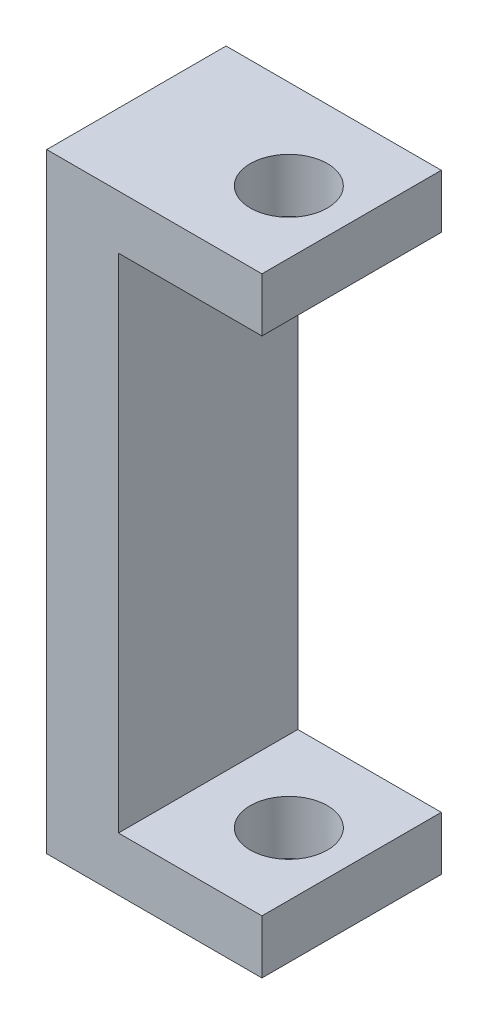
SolidWorks part; units mm, degrees
ref_plane "Front Plane" through (0, 0, 0) normal (0, 0, 1) x (1, 0, 0)
ref_plane "Top Plane" through (0, 0, 0) normal (0, 1, 0) x (1, 0, 0)
ref_plane "Right Plane" through (0, 0, 0) normal (1, 0, 0) x (0, 0, -1)
sketch "Sketch1" plane through (0, 0, 0) normal (0, 0, 1) x (1, 0, 0)
  line L1 (6, -17) -> (-6, -17)
  line L2 (6, -17) -> (6, 17)
  line L3 (6, 17) -> (-6, 17)
  line L4 (-6, -17) -> (-6, 17)
  line L5 (6, -17) -> (-6, 17) construction
  line L6 (6, 17) -> (-6, -17) construction
  point P0 (0, 0)
  dimension "D1" = 34
  dimension "D2" = 12
extrude "Boss-Extrude1" add sketch "Sketch1" along normal mid plane 10
sketch "Sketch2" plane through (0, 0, 5) normal (0, 0, 1) x (1, 0, 0)
  line L0 (6, -17) -> (6, 17) construction
  line L1 (-2, 14) -> (14, 14)
  line L2 (-2, 14) -> (-2, -14)
  line L3 (-2, -14) -> (14, -14)
  line L4 (14, 14) -> (14, -14)
  line L5 (-2, 14) -> (14, -14) construction
  line L6 (-2, -14) -> (14, 14) construction
  point P0 (6, 0)
  dimension "D1" = 28
  dimension "D2" = 8
extrude "Cut-Extrude1" cut sketch "Sketch2" against normal through all and the other way through all
sketch "Sketch3" plane through (0, 17, 0) normal (0, 1, 0) x (1, 0, 0)
  line L0 (6, -5) -> (6, 5) construction
  circle A0 centre (2.5, 0) radius 2.15
  dimension "D1" = 4.3
  dimension "D2" = 3.5
extrude "Cut-Extrude2" cut sketch "Sketch3" against normal through all contours A0
